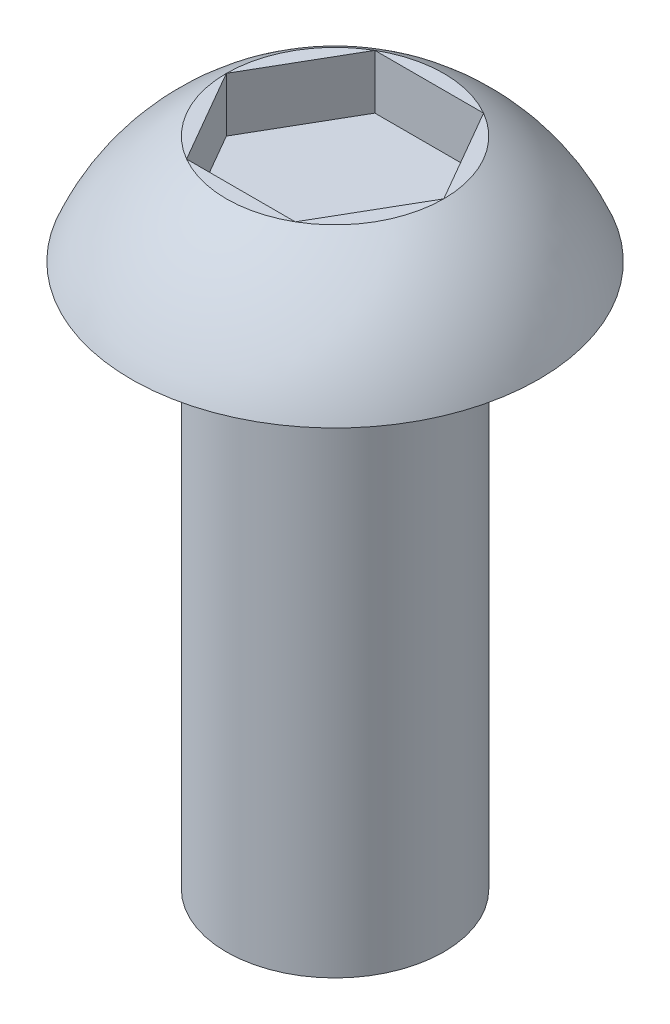
SolidWorks part; units mm, degrees
ref_plane "Front Plane" through (0, 0, 0) normal (0, 0, 1) x (1, 0, 0)
ref_plane "Top Plane" through (0, 0, 0) normal (0, 1, 0) x (1, 0, 0)
ref_plane "Right Plane" through (0, 0, 0) normal (1, 0, 0) x (0, 0, -1)
sketch "Sketch1" plane through (0, 0, 0) normal (0, 0, 1) x (1, 0, 0)
  line L0 (0, -310.2059) -> (0, 15200.0892) construction
  line L1 (0, 0) -> (2, 0)
  line L2 (2, 0) -> (2, 10)
  line L3 (2, 10) -> (3.75, 10)
  line L4 (0, 12) -> (2, 12)
  line L5 (0, 12) -> (0, 0)
  arc A0 (2, 12) -> (3.75, 10) centre (0, 8.4844) cw
  dimension "D1" = 4
  dimension "D2" = 10
  dimension "D3" = 7.5
  dimension "D4" = 4
  dimension "D5" = 2
revolve "Revolve1" add sketch "Sketch1" angle 360 about L0
sketch "Sketch2" plane through (0, 12, 0) normal (0, 1, 0) x (1, 0, 0)
  line L1 (2, 0) -> (1, 1.7321)
  line L2 (1, 1.7321) -> (-1, 1.7321)
  line L3 (-1, 1.7321) -> (-2, 0)
  line L4 (-2, 0) -> (-1, -1.7321)
  line L5 (-1, -1.7321) -> (1, -1.7321)
  line L6 (1, -1.7321) -> (2, 0)
  circle A0 centre (0, 0) radius 1.7321 construction
  circle A1 centre (0, 0) radius 2 construction
extrude "Cut-Extrude1" cut sketch "Sketch2" against normal blind 1
